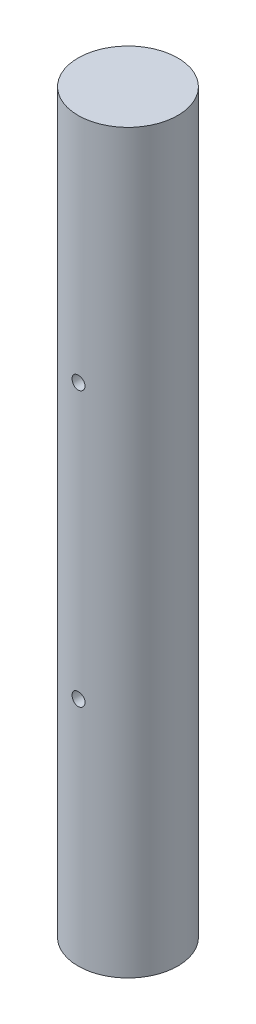
SolidWorks part; units mm, degrees
material "Maple"
ref_plane "Front Plane" through (0, 0, 0) normal (0, 0, 1) x (1, 0, 0)
ref_plane "Top Plane" through (0, 0, 0) normal (0, 1, 0) x (1, 0, 0)
ref_plane "Right Plane" through (0, 0, 0) normal (1, 0, 0) x (0, 0, -1)
sketch "Sketch2" plane through (0, 0, 0) normal (0, 1, 0) x (1, 0, 0)
  circle A0 centre (0, 0) radius 11.5
  dimension "D1" = 23
extrude "Boss-Extrude1" add sketch "Sketch2" along normal blind 170
sketch "Sketch3" plane through (0, 0, 0) normal (0, 0, 1) x (1, 0, 0)
  line L0 (-11.5, 53.38) -> (11.5, 53.38) construction
  line L1 (-11.5, 170) -> (-11.5, 0) construction
  line L2 (11.5, 0) -> (11.5, 170) construction
  line L3 (-11.5, 0) -> (11.5, 0) construction
  line L4 (-11.5, 85) -> (11.5, 85) construction
  line L5 (-11.5, 116.62) -> (11.5, 116.62) construction
  circle A0 centre (0, 53.38) radius 1.5
  circle A1 centre (0, 116.62) radius 1.5
  dimension "D2" = 3
  dimension "D1" = 53.38
extrude "Cut-Extrude1" cut sketch "Sketch3" along normal up to surface (11.4018 mm away)
